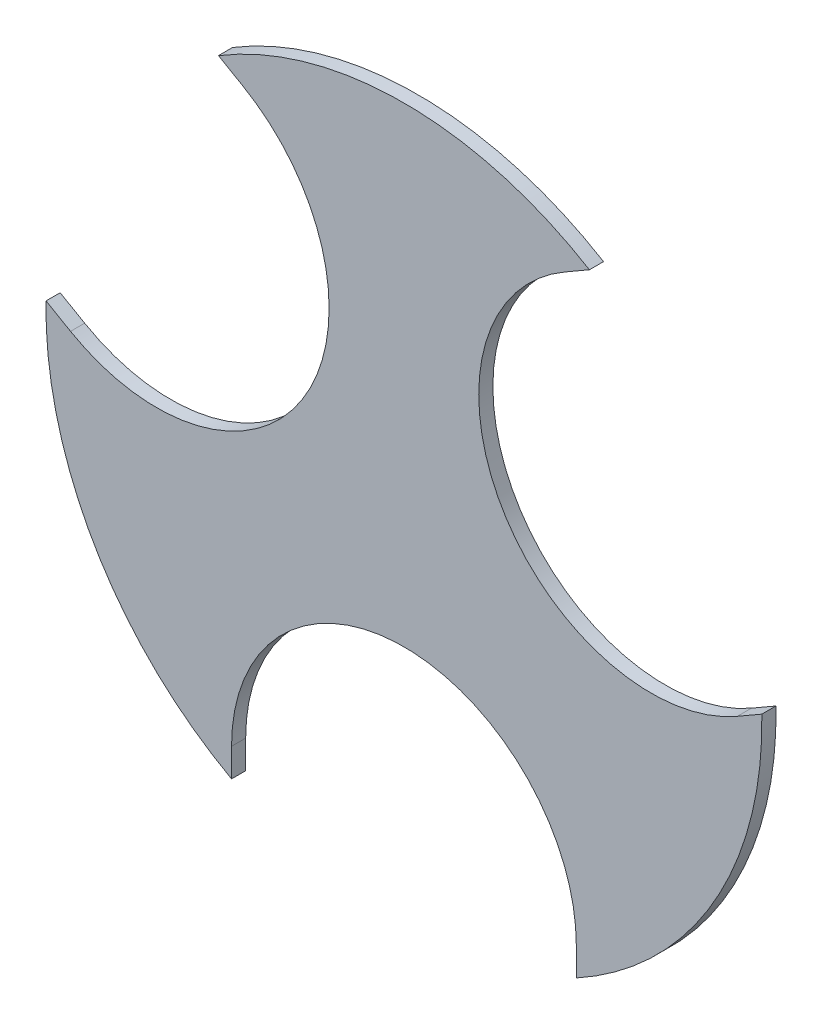
SolidWorks part; units mm, degrees
ref_plane "Front Plane" through (0, 0, 0) normal (0, 0, 1) x (1, 0, 0)
ref_plane "Top Plane" through (0, 0, 0) normal (0, 1, 0) x (1, 0, 0)
ref_plane "Right Plane" through (0, 0, 0) normal (1, 0, 0) x (0, 0, -1)
sketch "Sketch1" plane through (0, 0, 0) normal (0, 0, 1) x (1, 0, 0)
  line L0 (-87.4686, 50.5) -> (87.4686, 50.5) construction
  line L1 (87.4686, 50.5) -> (0, -101) construction
  line L2 (0, -101) -> (-87.4686, 50.5) construction
  line L3 (0, -101) -> (0, 50.5) construction
  line L4 (-87.4686, 50.5) -> (43.7343, -25.25) construction
  line L5 (-56.9686, 103.3275) -> (-117.9686, -2.3275) construction
  line L6 (-61, -101) -> (61, -101) construction
  line L7 (56.9686, 103.3275) -> (117.9686, -2.3275) construction
  line L8 (87.4686, 50.5) -> (-43.7343, -25.25) construction
  line L9 (-65.6288, 108.3275) -> (-56.9686, 103.3275)
  line L10 (-126.6288, 2.6725) -> (-117.9686, -2.3275)
  line L11 (65.6288, 108.3275) -> (56.9686, 103.3275)
  line L12 (117.9686, -2.3275) -> (126.6288, 2.6725)
  line L14 (-61, -101) -> (-61, -111)
  line L15 (61, -101) -> (61, -111)
  arc A0 (-117.9686, -2.3275) -> (-56.9686, 103.3275) centre (-87.4686, 50.5) ccw
  arc A1 (61, -101) -> (-61, -101) centre (0, -101) ccw
  arc A2 (56.9686, 103.3275) -> (117.9686, -2.3275) centre (87.4686, 50.5) ccw
  arc A3 (65.6288, 108.3275) -> (-65.6288, 108.3275) centre (0, 0) ccw
  arc A5 (-126.6288, 2.6725) -> (-61, -111) centre (0, 0) ccw
  circle A6 centre (0, 0) radius 40 construction
  arc A9 (61, -111) -> (126.6288, 2.6725) centre (0, 0) ccw
  point P8 (-117.9686, -2.3275)
  dimension "D1" = 122
  dimension "D2" = 10
  dimension "D3" = 10
  dimension "D4" = 80
  dimension "D5" = 10
  dimension "D6" = 122
extrude "Boss-Extrude2" add sketch "Sketch1" along normal blind 5
